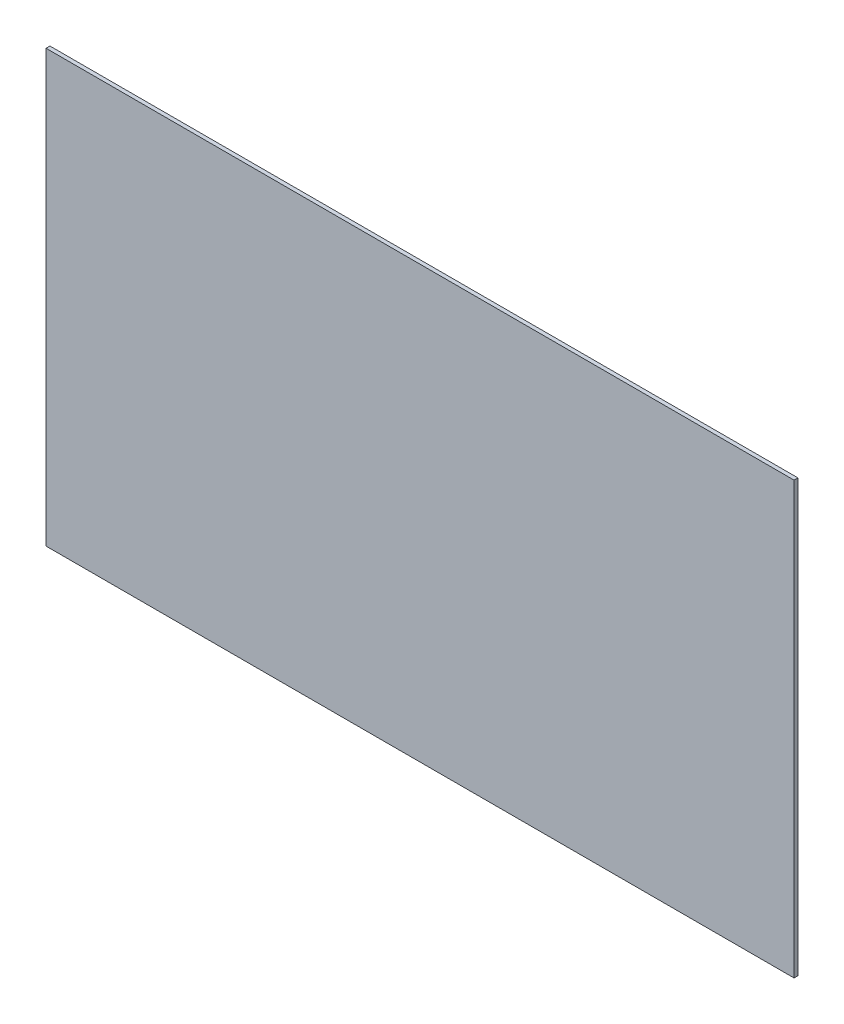
SolidWorks part; units mm, degrees
material "Acrylic (Medium-high impact)"
ref_plane "Front Plane" through (0, 0, 0) normal (0, 0, 1) x (1, 0, 0)
ref_plane "Top Plane" through (0, 0, 0) normal (0, 1, 0) x (1, 0, 0)
ref_plane "Right Plane" through (0, 0, 0) normal (1, 0, 0) x (0, 0, -1)
sketch "Sketch1" plane through (0, 0, 0) normal (0, 0, 1) x (1, 0, 0)
  line L1 (0, 0) -> (1828.8, 0)
  line L2 (0, 0) -> (0, 1054.1)
  line L3 (0, 1054.1) -> (1828.8, 1054.1)
  line L4 (1828.8, 0) -> (1828.8, 1054.1)
  dimension "D1" = 1054.1
  dimension "D2" = 1828.8
extrude "Boss-Extrude1" add sketch "Sketch1" along normal blind 9.525
